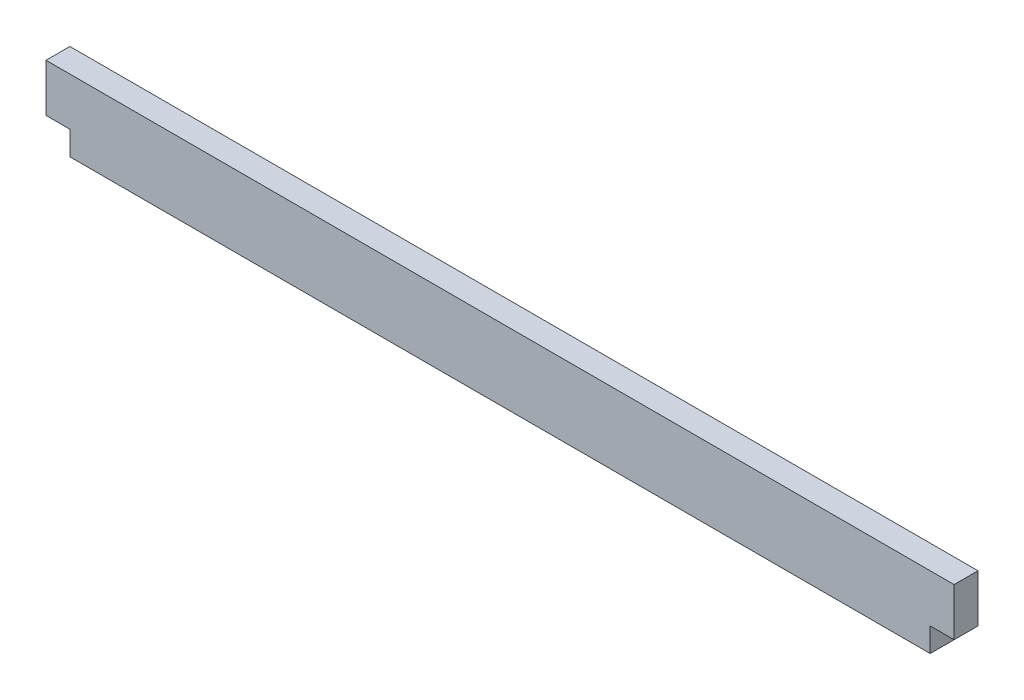
SolidWorks part; units mm, degrees
ref_plane "Front Plane" through (0, 0, 0) normal (0, 0, 1) x (1, 0, 0)
ref_plane "Top Plane" through (0, 0, 0) normal (0, 1, 0) x (1, 0, 0)
ref_plane "Right Plane" through (0, 0, 0) normal (1, 0, 0) x (0, 0, -1)
sketch "Sketch1" plane through (0, 0, 0) normal (0, 0, 1) x (1, 0, 0)
  line L0 (31.5772, 9.525) -> (31.5772, 0) construction
  line L1 (88.7272, 0) -> (-25.5728, 0)
  line L2 (91.9022, 3.175) -> (91.9022, 9.525)
  line L3 (91.9022, 9.525) -> (-28.7478, 9.525)
  line L4 (-28.7478, 3.175) -> (-28.7478, 9.525)
  line L5 (91.9022, 3.175) -> (88.7272, 3.175)
  line L6 (88.7272, 0) -> (88.7272, 3.175)
  line L7 (-28.7478, 3.175) -> (-25.5728, 3.175)
  line L8 (-25.5728, 0) -> (-25.5728, 3.175)
  dimension "D1" = 3.175
  dimension "D2" = 3.175
  dimension "D3" = 9.525
  dimension "D4" = 114.3
extrude "Boss-Extrude1" add sketch "Sketch1" along normal blind 3.175
